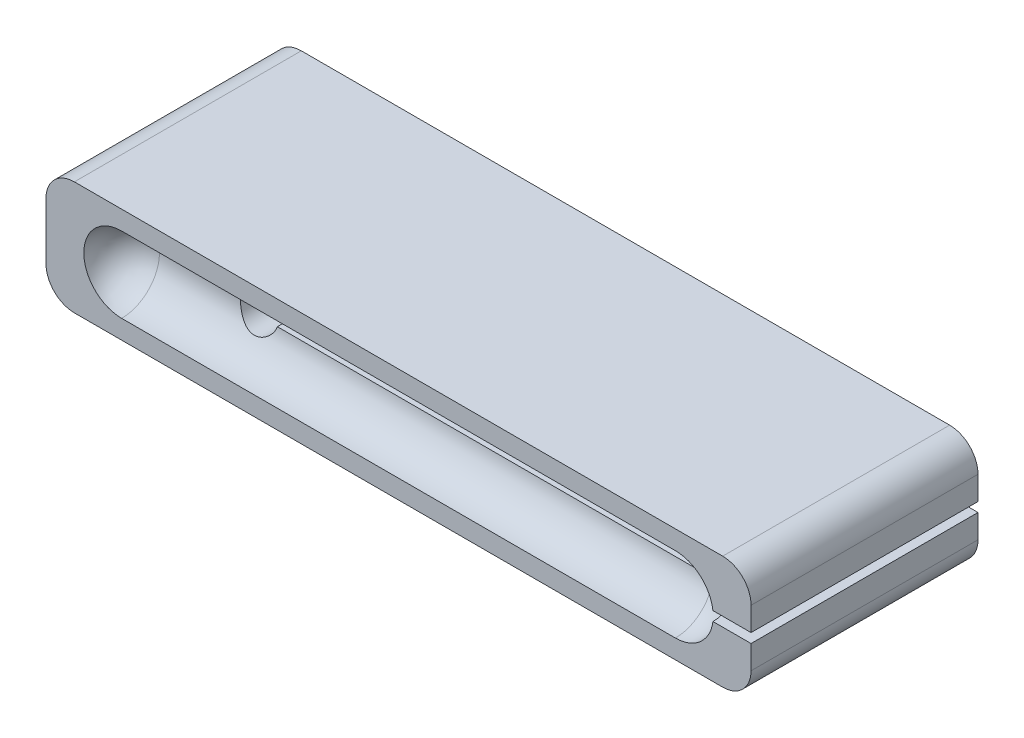
SolidWorks part; units mm, degrees
material "Pine"
ref_plane "Front Plane" through (0, 0, 0) normal (0, 0, 1) x (1, 0, 0)
ref_plane "Top Plane" through (0, 0, 0) normal (0, 1, 0) x (1, 0, 0)
ref_plane "Right Plane" through (0, 0, 0) normal (1, 0, 0) x (0, 0, -1)
sketch "Sketch1" plane through (0, 0, 0) normal (0, 0, 1) x (1, 0, 0)
  line L0 (0, 20.6375) -> (0, 28.575)
  line L1 (-9.525, 0) -> (-227.203, 0)
  line L2 (0, 9.525) -> (0, 17.4625)
  line L3 (-9.525, 38.1) -> (-227.203, 38.1)
  line L4 (-236.728, 9.525) -> (-236.728, 28.575)
  line L5 (0, 20.6375) -> (-22.6504, 20.6375)
  line L6 (-28.1496, 17.4625) -> (-171.6516, 17.4625)
  line L7 (0, 17.4625) -> (-22.6504, 17.4625)
  line L9 (-28.1496, 20.6375) -> (-171.6516, 20.6375)
  arc A0 (0, 28.575) -> (-9.525, 38.1) centre (-9.525, 28.575) ccw
  arc A1 (-9.525, 0) -> (0, 9.525) centre (-9.525, 9.525) ccw
  arc A2 (-227.203, 0) -> (-236.728, 9.525) centre (-227.203, 9.525) cw
  arc A3 (-227.203, 38.1) -> (-236.728, 28.575) centre (-227.203, 28.575) ccw
  arc A4 (-22.6504, 20.6375) -> (-28.1496, 20.6375) centre (-25.4, 19.05) ccw
  arc A5 (-28.1496, 17.4625) -> (-22.6504, 17.4625) centre (-25.4, 19.05) ccw
  arc A6 (-171.6516, 20.6375) -> (-171.6516, 17.4625) centre (-177.8, 19.05) ccw
  point P7 (0, 38.1)
  point P10 (0, 0)
  point P13 (-236.728, 0)
  dimension "D3" = 9.525
  dimension "D4" = 6.35
  dimension "D10" = 12.7
  dimension "D1" = 38.1
  dimension "D2" = 236.728
  dimension "D5" = 19.05
  dimension "D6" = 25.4
  dimension "D7" = 19.05
  dimension "D8" = 17.4625
  dimension "D9" = 177.8
extrude "Boss-Extrude1" add sketch "Sketch1" along normal blind 76.2 contours L3 A3 L4 A2 L1 A1 L2 L7 A5 L6 A6 L9 A4 L5 L0 A0
sketch "Sketch2" plane through (0, 0, 76.2) normal (0, 0, 1) x (1, 0, 0)
  line L0 (-224.028, 19.05) -> (-12.7, 19.05) construction
  line L1 (-211.328, 31.75) -> (-25.4, 31.75)
  line L2 (-236.728, 9.525) -> (-236.728, 28.575) construction
  line L3 (0, 20.6375) -> (0, 28.575) construction
  line L4 (-224.028, 19.05) -> (-12.7, 19.05)
  arc A0 (-224.028, 19.05) -> (-211.328, 31.75) centre (-211.328, 19.05) cw
  arc A1 (-12.7, 19.05) -> (-25.4, 31.75) centre (-25.4, 19.05) ccw
  point P8 (0, 24.6062)
  point P11 (-236.728, 19.05)
  dimension "D1" = 12.7
  dimension "D2" = 12.7
  dimension "D3" = 25.4
  dimension "D4" = 25.4
  dimension "D5" = 12.7
revolve "Cut-Revolve1" cut sketch "Sketch2" angle 360 about L0
sketch "Sketch4" plane through (0, 0, 0) normal (0, 0, -1) x (-1, 0, 0)
  line L0 (224.028, 19.05) -> (12.7, 19.05) construction
  line L1 (25.4, 31.75) -> (211.328, 31.75)
  line L2 (236.728, 9.525) -> (236.728, 28.575) construction
  line L3 (9.525, 38.1) -> (227.203, 38.1) construction
  line L4 (0, 9.525) -> (0, 17.4625) construction
  line L5 (224.028, 19.05) -> (12.7, 19.05)
  arc A0 (12.7, 19.05) -> (25.4, 31.75) centre (25.4, 19.05) cw
  arc A1 (224.028, 19.05) -> (211.328, 31.75) centre (211.328, 19.05) ccw
  point P11 (0, 13.4938)
  point P14 (236.728, 19.05)
  dimension "D3" = 12.7
  dimension "D1" = 19.05
  dimension "D2" = 12.7
  dimension "D4" = 12.7
revolve "Cut-Revolve3" cut sketch "Sketch4" angle 360 about L0
